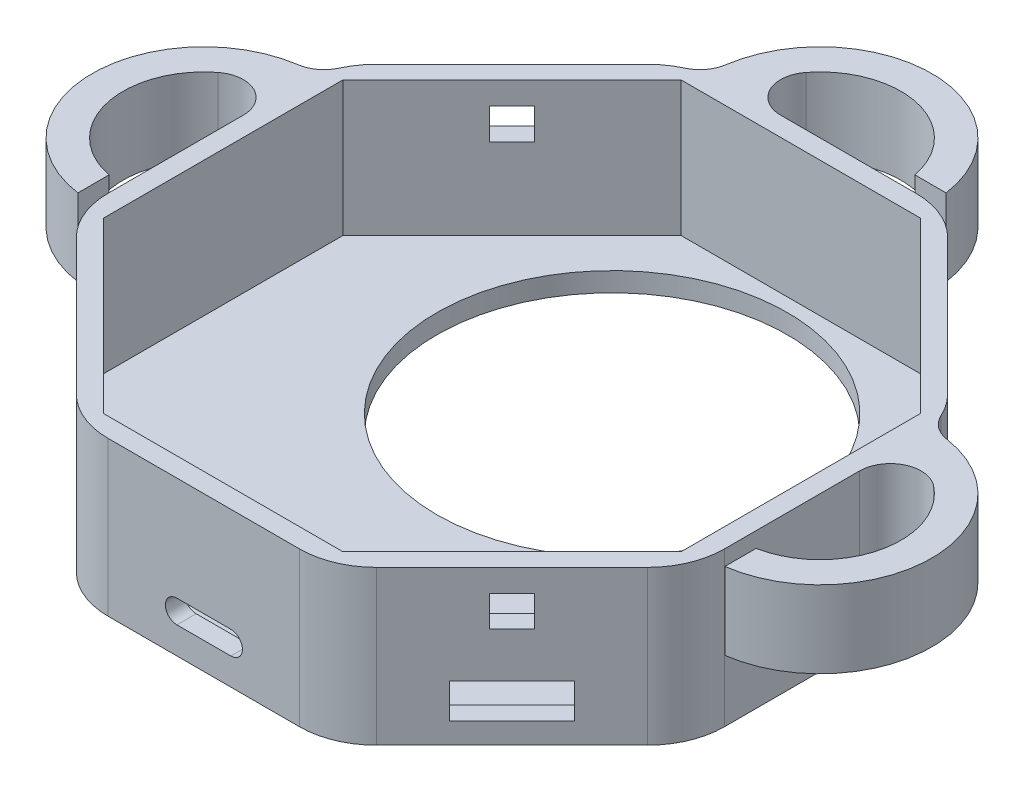
SolidWorks part; units mm, degrees
other "DetailItem5"
other "DetailItem6"
other "DetailItem7"
other "DetailItem8"
other "DetailItem9"
other "DetailItem10"
ref_plane "Front Plane" through (0, 0, 0) normal (0, 0, 1) x (1, 0, 0)
ref_plane "Top Plane" through (0, 0, 0) normal (0, 1, 0) x (1, 0, 0)
ref_plane "Right Plane" through (0, 0, 0) normal (1, 0, 0) x (0, 0, -1)
sketch "Sketch1" plane through (0, 0, 0) normal (0, 1, 0) x (1, 0, 0)
  line L1 (16.5685, 40) -> (-16.5685, 40)
  line L2 (-16.5685, 40) -> (-40, 16.5685)
  line L3 (-40, 16.5685) -> (-40, -16.5685)
  line L4 (-40, -16.5685) -> (-16.5685, -40)
  line L5 (-16.5685, -40) -> (16.5685, -40)
  line L6 (16.5685, -40) -> (40, -16.5685)
  line L7 (40, -16.5685) -> (40, 16.5685)
  line L8 (40, 16.5685) -> (16.5685, 40)
  circle A0 centre (0, 0) radius 40 construction
  point P1 (0, 40)
  dimension "D1" = 80
extrude "Boss-Extrude1" add sketch "Sketch1" along normal blind 20
ref_plane "Plane1" through (0, 15, 0) normal (0, 1, 0) x (1, 0, 0)
sketch "Sketch5" plane through (40, 0, 0) normal (1, 0, 0) x (0, 0, -1)
  line L0 (-12.5, 15) -> (12.5, 15) construction
  line L1 (-16.5685, 20) -> (16.5685, 20) construction
  line L2 (-14.5, 10) -> (-10.5, 10)
  line L3 (-14.5, 10) -> (-14.5, 20)
  line L4 (-14.5, 20) -> (-10.5, 20)
  line L5 (-10.5, 10) -> (-10.5, 20)
  line L6 (-14.5, 10) -> (-10.5, 20) construction
  line L7 (-14.5, 20) -> (-10.5, 10) construction
  line L9 (10.5, 10) -> (14.5, 10)
  line L10 (10.5, 10) -> (10.5, 20)
  line L11 (10.5, 20) -> (14.5, 20)
  line L12 (14.5, 10) -> (14.5, 20)
  line L13 (10.5, 10) -> (14.5, 20) construction
  line L14 (10.5, 20) -> (14.5, 10) construction
  point P6 (0, 15)
  dimension "D1" = 4
  dimension "D2" = 4
  dimension "D3" = 25
  dimension "D4" = 15
sketch "Sketch7" plane through (0, 15, 0) normal (0, 1, 0) x (1, 0, 0)
  line L11 (40, -14.5) -> (40, -10.5) construction
  line L12 (40, -12.5) -> (40, 12.5) construction
  line L13 (40, 10.5) -> (40, 14.5) construction
  line L14 (40, 10.5) -> (40, 14.5) construction
  arc A0 (40, -10.5) -> (40, 10.5) centre (40, 0) ccw
  dimension "D1" = 10.5
sweep "Sweep9" add profiles "Sketch5" path "Sketch7"
sketch "Sketch16" plane through (0, 20, 0) normal (0, 1, 0) x (1, 0, 0)
  line L1 (40, -14.5) -> (42, -14.5)
  line L2 (42, -14.5) -> (42, -10)
  line L3 (42, -10) -> (40, -10)
  line L4 (40, -10.5) -> (40, 10.5) construction
  line L5 (40, -10) -> (40, -14.5)
  dimension "D1" = 2
  dimension "D2" = 4.5
extrude "Cut-Extrude9" cut sketch "Sketch16" against normal up to surface (10 mm away) up to face at (46.25, 10, 0)
mirror "Mirror1" about plane through (0, 0, 0) normal (1, 0, 0) of "Cut-Extrude9", "Sweep9"
sketch "Sketch19" plane through (0, 0, -40) normal (0, 0, -1) x (-1, 0, 0)
  line L0 (-12.5, 15) -> (12.5, 15) construction
  line L1 (44, 15) -> (-44, 15) construction
  line L2 (-16.5685, 20) -> (16.5685, 20) construction
  line L3 (-14.5, 10) -> (-10.5, 10)
  line L4 (-14.5, 10) -> (-14.5, 20)
  line L5 (-14.5, 20) -> (-10.5, 20)
  line L6 (-10.5, 10) -> (-10.5, 20)
  line L7 (-14.5, 10) -> (-10.5, 20) construction
  line L8 (-14.5, 20) -> (-10.5, 10) construction
  line L10 (10.5, 10) -> (14.5, 10)
  line L11 (10.5, 10) -> (10.5, 20)
  line L12 (10.5, 20) -> (14.5, 20)
  line L13 (14.5, 10) -> (14.5, 20)
  line L14 (10.5, 10) -> (14.5, 20) construction
  line L15 (10.5, 20) -> (14.5, 10) construction
  point P14 (0, 15)
  dimension "D1" = 25
  dimension "D2" = 4
  dimension "D3" = 4
sketch "Sketch20" plane through (0, 15, 0) normal (0, 1, 0) x (1, 0, 0)
  line L0 (10.5, 40) -> (-10.5, 40) construction
  line L1 (14.5, 40) -> (10.5, 40) construction
  line L2 (12.5, 40) -> (-12.5, 40) construction
  line L3 (-10.5, 40) -> (-14.5, 40) construction
  line L4 (-10.5, 40) -> (-14.5, 40) construction
  line L5 (16.5685, 40) -> (-16.5685, 40) construction
  arc A0 (10.5, 40) -> (-10.5, 40) centre (0, 40) ccw
sweep "Sweep10" add profiles "Sketch19" path "Sketch20"
sketch "Sketch6" plane through (0, 20, 0) normal (0, 1, 0) x (1, 0, 0)
  line L1 (-15.533, -37.5) -> (15.533, -37.5)
  line L2 (15.533, -37.5) -> (37.5, -15.533)
  line L3 (37.5, -15.533) -> (37.5, 15.533)
  line L4 (37.5, 15.533) -> (15.533, 37.5)
  line L5 (15.533, 37.5) -> (-15.533, 37.5)
  line L6 (-15.533, 37.5) -> (-37.5, 15.533)
  line L7 (-37.5, 15.533) -> (-37.5, -15.533)
  line L8 (-37.5, -15.533) -> (-15.533, -37.5)
  circle A0 centre (0, 0) radius 37.5 construction
  point P1 (0, -37.5)
  dimension "D1" = 75
extrude "Cut-Extrude4" cut sketch "Sketch6" against normal blind 17.5
sketch "Sketch21" plane through (0, 20, 0) normal (0, 1, 0) x (1, 0, 0)
  line L0 (14.5, 40) -> (14.5, 42)
  line L1 (14.5, 42) -> (10, 42)
  line L2 (10, 42) -> (10, 40)
  line L3 (10.5, 40) -> (-10.5, 40) construction
  line L4 (10, 40) -> (14.5, 40)
  dimension "D1" = 4.5
  dimension "D2" = 2
sketch "Sketch3" plane through (0, 0, 40) normal (0, 0, 1) x (1, 0, 0)
  line L0 (-3.5, 5) -> (3.5, 5) construction
  line L1 (-3.5, 6.5) -> (3.5, 6.5)
  line L2 (-3.5, 3.5) -> (3.5, 3.5)
  arc A0 (-3.5, 6.5) -> (-3.5, 3.5) centre (-3.5, 5) ccw
  arc A1 (3.5, 3.5) -> (3.5, 6.5) centre (3.5, 5) ccw
  point P2 (0, 5)
  point P7 (-5, 5)
  point P8 (5, 5)
  dimension "D1" = 10
  dimension "D2" = 3
  dimension "D3" = 5
extrude "Cut-Extrude5" cut sketch "Sketch3" against normal up to surface (2.5 mm away) up to face at (0, 11.25, 37.5)
sketch "Sketch15" plane through (28.2843, 0, 28.2843) normal (0.7071, 0, 0.7071) x (0.7071, 0, -0.7071)
  line L1 (-5.75, 2.75) -> (5.75, 2.75)
  line L2 (-5.75, 2.75) -> (-5.75, 7.25)
  line L3 (-5.75, 7.25) -> (5.75, 7.25)
  line L4 (5.75, 2.75) -> (5.75, 7.25)
  line L5 (-5.75, 2.75) -> (5.75, 7.25) construction
  line L6 (-5.75, 7.25) -> (5.75, 2.75) construction
  point P0 (0, 5)
  dimension "D1" = 4.5
  dimension "D2" = 11.5
  dimension "D3" = 5
extrude "Cut-Extrude8" cut sketch "Sketch15" against normal up to surface (2.5 mm away) up to face at (26.5165, 11.25, 26.5165)
sketch "Sketch17" plane through (-28.2843, 0, 28.2843) normal (-0.7071, 0, 0.7071) x (0.7071, 0, 0.7071)
  line L1 (-7, 3.5) -> (7, 3.5)
  line L2 (-7, 3.5) -> (-7, 6.5)
  line L3 (-7, 6.5) -> (7, 6.5)
  line L4 (7, 3.5) -> (7, 6.5)
  line L5 (-7, 3.5) -> (7, 6.5) construction
  line L6 (-7, 6.5) -> (7, 3.5) construction
  point P0 (0, 5)
  point P5 (0, 6.5)
  dimension "D1" = 14
  dimension "D2" = 3
  dimension "D3" = 5
extrude "Cut-Extrude10" cut sketch "Sketch17" against normal up to surface (2.5 mm away) up to face at (-26.5165, 11.25, 26.5165)
extrude "Cut-Extrude11" cut sketch "Sketch21" against normal up to surface (10 mm away) up to face at (0, 10, -46.25)
sketch "Sketch22" plane through (28.2843, 0, -28.2843) normal (0.7071, 0, -0.7071) x (-0.7071, 0, -0.7071)
  line L0 (51.975, 0) -> (-51.975, 0) construction
  circle A0 centre (0, 10) radius 2
  dimension "D1" = 4
  dimension "D2" = 10
extrude "Cut-Extrude12" cut sketch "Sketch22" against normal up to surface (2.5 mm away) up to face at (26.5165, 11.25, -26.5165)
fillet "Fillet1" radius 10 8 edges at (-40, 10, -16.5685) (-16.5685, 10, -40) (16.5685, 10, -40) (40, 10, -16.5685) (-40, 10, 16.5685) (40, 10, 16.5685) (16.5685, 10, 40) (-16.5685, 10, 40)
fillet "Fillet2" radius 4 6 edges at (-39.783, 15, -14.4984) (-40, 15, -10.5) (-14.4984, 15, -39.783) (-10.5, 15, -40) (39.783, 15, -14.4984) (40, 15, -10.5)
sketch "Sketch24" plane through (-28.2843, 0, 28.2843) normal (-0.7071, 0, 0.7071) x (0.7071, 0, 0.7071)
  line L0 (-12.4264, 20) -> (12.4264, 20) construction
  line L1 (-2.05, 13.05) -> (2.05, 13.05)
  line L2 (-2.05, 13.05) -> (-2.05, 17.05)
  line L3 (-2.05, 17.05) -> (2.05, 17.05)
  line L4 (2.05, 13.05) -> (2.05, 17.05)
  line L5 (-2.05, 13.05) -> (2.05, 17.05) construction
  line L6 (-2.05, 17.05) -> (2.05, 13.05) construction
  point P0 (0, 15.05)
  dimension "D1" = 2.95
  dimension "D2" = 4
  dimension "D3" = 4.1
extrude "Cut-Extrude14" cut sketch "Sketch24" against normal up to surface (77.5 mm away)
ref_plane "Plane2" through (0, 0, 0) normal (-0.7071, 0, 0.7071) x (0.7071, 0, 0.7071)
mirror "Mirror2" about plane through (0, 0, 0) normal (-0.7071, 0, 0.7071) of "Cut-Extrude14"
sketch "Sketch28" plane through (28.2843, 0, 28.2843) normal (0.7071, 0, 0.7071) x (0.7071, 0, -0.7071)
  line L0 (-12.4264, 20) -> (12.4264, 20) construction
  line L1 (-2.05, 13.05) -> (2.05, 13.05)
  line L2 (-2.05, 13.05) -> (-2.05, 17.05)
  line L3 (-2.05, 17.05) -> (2.05, 17.05)
  line L4 (2.05, 13.05) -> (2.05, 17.05)
  line L5 (-2.05, 13.05) -> (2.05, 17.05) construction
  line L6 (-2.05, 17.05) -> (2.05, 13.05) construction
  point P0 (0, 15.05)
  dimension "D1" = 2.95
  dimension "D2" = 4.1
  dimension "D3" = 4
extrude "Cut-Extrude15" cut sketch "Sketch28" against normal up to surface (77.5 mm away)
ref_plane "Plane3" through (0, 0, 0) normal (0.7071, 0, 0.7071) x (0.7071, 0, -0.7071)
mirror "Mirror3" about plane through (0, 0, 0) normal (0.7071, 0, 0.7071) of "Cut-Extrude15"
sketch "Sketch23" plane through (0, 2.5, 0) normal (0, 1, 0) x (1, 0, 0)
  line L0 (0, 13) -> (0, -30.25) construction
  line L1 (7.0116, 35.75) -> (-7.0116, 35.75) construction
  circle A0 centre (0, 13) radius 22.75
  point P2 (0, 35.75)
  dimension "D1" = 45.5
  dimension "D2" = 66
  dimension "D3" = 13
extrude "Cut-Extrude13" cut sketch "Sketch23" against normal up to surface (2.5 mm away) up to face at (0, 0, 0)
